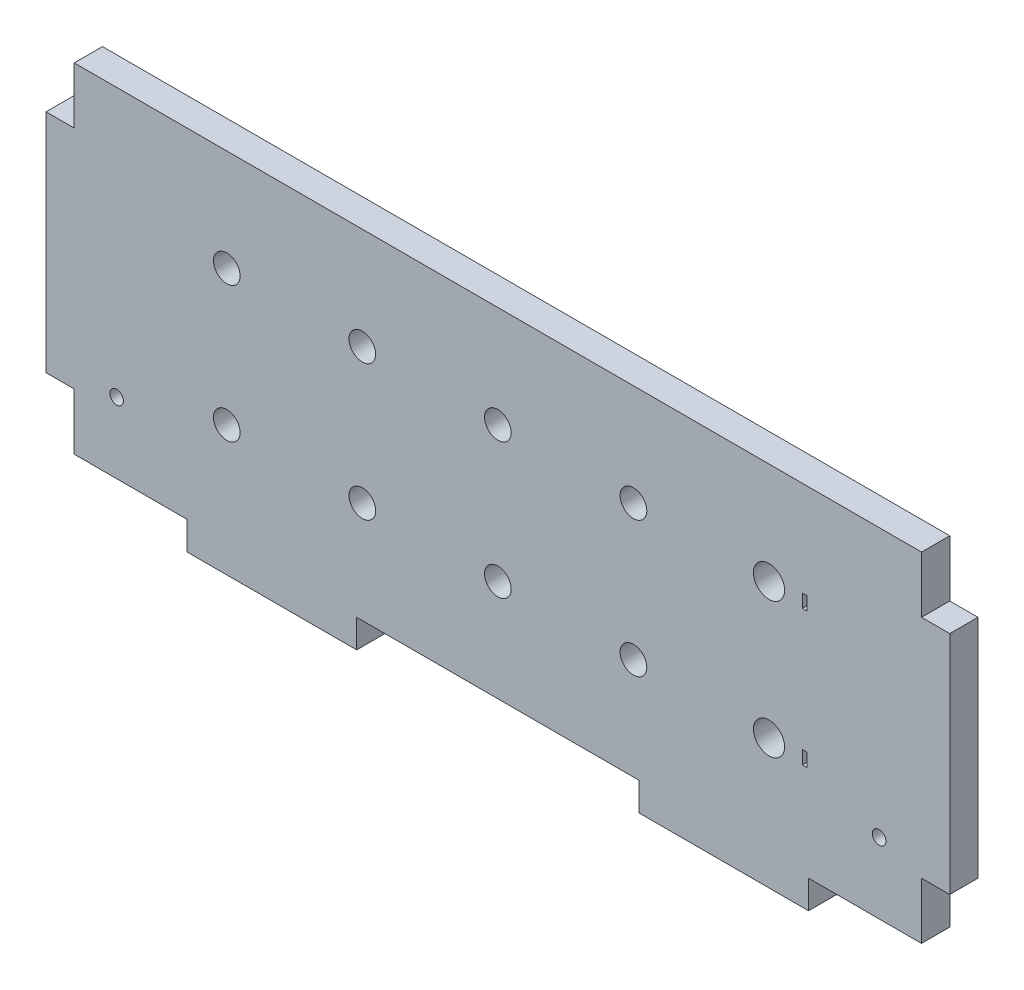
SolidWorks part; units mm, degrees
ref_plane "Front Plane" through (0, 0, 0) normal (0, 0, 1) x (1, 0, 0)
ref_plane "Top Plane" through (0, 0, 0) normal (0, 1, 0) x (1, 0, 0)
ref_plane "Right Plane" through (0, 0, 0) normal (1, 0, 0) x (0, 0, -1)
sketch "Sketch1" plane through (0, 0, 0) normal (0, 0, 1) x (1, 0, 0)
  line L1 (-95.25, -38.1) -> (95.25, -38.1)
  line L2 (-95.25, -38.1) -> (-95.25, 38.1)
  line L3 (-95.25, 38.1) -> (95.25, 38.1)
  line L4 (95.25, -38.1) -> (95.25, 38.1)
  line L5 (-95.25, -38.1) -> (95.25, 38.1) construction
  line L6 (-95.25, 38.1) -> (95.25, -38.1) construction
  point P0 (0, 0)
  dimension "D1" = 190.5
  dimension "D2" = 76.2
extrude "Boss-Extrude1" add sketch "Sketch1" along normal blind 6.35
sketch "Sketch2" plane through (-95.25, 0, 0) normal (-1, 0, 0) x (0, 0, 1)
  line L0 (0, 38.1) -> (0, -38.1) construction
  line L1 (0, 25.4) -> (6.35, 25.4)
  line L2 (0, 25.4) -> (0, -25.4)
  line L3 (0, -25.4) -> (6.35, -25.4)
  line L4 (6.35, 25.4) -> (6.35, -25.4)
  line L5 (6.35, 38.1) -> (6.35, -38.1) construction
  line L6 (6.35, 38.1) -> (0, 38.1) construction
  line L7 (6.35, -38.1) -> (0, -38.1) construction
  dimension "D1" = 12.7
  dimension "D2" = 12.7
extrude "Boss-Extrude2" add sketch "Sketch2" along normal blind 6.35
sketch "Sketch3" plane through (95.25, 0, 0) normal (1, 0, 0) x (0, 0, -1)
  line L0 (-6.35, -38.1) -> (-6.35, 38.1) construction
  line L1 (-6.35, 25.4) -> (0, 25.4)
  line L2 (-6.35, 25.4) -> (-6.35, -25.4)
  line L3 (-6.35, -25.4) -> (0, -25.4)
  line L4 (0, 25.4) -> (0, -25.4)
  line L5 (0, -38.1) -> (0, 38.1) construction
  line L6 (-6.35, 38.1) -> (0, 38.1) construction
  line L7 (-6.35, -38.1) -> (0, -38.1) construction
  dimension "D1" = 12.7
  dimension "D2" = 12.7
extrude "Boss-Extrude3" add sketch "Sketch3" along normal blind 6.35
sketch "Sketch4" plane through (0, -38.1, 0) normal (0, -1, 0) x (1, 0, 0)
  line L0 (-95.25, 6.35) -> (95.25, 6.35) construction
  line L1 (-69.85, 6.35) -> (-31.75, 6.35)
  line L2 (-69.85, 6.35) -> (-69.85, 0)
  line L3 (-69.85, 0) -> (-31.75, 0)
  line L4 (-31.75, 6.35) -> (-31.75, 0)
  line L5 (-95.25, 0) -> (95.25, 0) construction
  line L6 (-95.25, 6.35) -> (-95.25, 0) construction
  line L7 (31.75, 6.35) -> (69.85, 6.35)
  line L8 (31.75, 6.35) -> (31.75, 0)
  line L9 (31.75, 0) -> (69.85, 0)
  line L10 (69.85, 6.35) -> (69.85, 0)
  line L11 (95.25, 6.35) -> (95.25, 0) construction
  point P14 (95.25, 3.175)
  dimension "D1" = 25.4
  dimension "D2" = 25.4
  dimension "D3" = 38.1
  dimension "D4" = 38.1
extrude "Boss-Extrude4" add sketch "Sketch4" along normal blind 6.35
sketch "Sketch7" plane through (0, 0, 0) normal (0, 0, -1) x (-1, 0, 0)
  line L0 (-30.48, 15.24) -> (0, 15.24) construction
  line L1 (-30.48, 15.24) -> (-30.48, -15.24) construction
  line L2 (-95.25, 38.1) -> (95.25, 38.1) construction
  line L3 (-60.96, 15.24) -> (-60.96, -15.24) construction
  line L5 (95.25, -38.1) -> (69.85, -38.1) construction
  line L6 (30.48, 15.24) -> (15.24, 15.24) construction
  line L7 (15.24, 15.24) -> (0, 15.24) construction
  line L8 (0, 15.24) -> (0, 38.1) construction
  line L9 (0, -15.24) -> (0, -38.1) construction
  line L10 (-95.25, -38.1) -> (-95.25, -25.4) construction
  line L11 (101.6, 25.4) -> (101.6, -25.4) construction
  line L12 (-60.96, 15.24) -> (-68.96, 15.24) construction
  line L13 (-68.46, 13.74) -> (-69.46, 13.74)
  line L14 (-68.46, 13.74) -> (-68.46, 16.74)
  line L15 (-68.46, 16.74) -> (-69.46, 16.74)
  line L16 (-69.46, 13.74) -> (-69.46, 16.74)
  line L17 (-68.46, 13.74) -> (-69.46, 16.74) construction
  line L18 (-68.46, 16.74) -> (-69.46, 13.74) construction
  line L19 (-68.96, -15.24) -> (-60.96, -15.24) construction
  line L20 (-69.46, -16.74) -> (-68.46, -16.74)
  line L21 (-69.46, -16.74) -> (-69.46, -13.74)
  line L22 (-69.46, -13.74) -> (-68.46, -13.74)
  line L23 (-68.46, -16.74) -> (-68.46, -13.74)
  line L24 (-69.46, -16.74) -> (-68.46, -13.74) construction
  line L25 (-69.46, -13.74) -> (-68.46, -16.74) construction
  circle A0 centre (-30.48, 15.24) radius 3
  circle A1 centre (0, 15.24) radius 3
  circle A2 centre (30.48, 15.24) radius 3
  circle A3 centre (60.96, 15.24) radius 3
  circle A4 centre (0, -15.24) radius 3
  circle A5 centre (30.48, -15.24) radius 3
  circle A6 centre (60.96, -15.24) radius 3
  circle A7 centre (-30.48, -15.24) radius 3
  circle A8 centre (-60.96, 15.24) radius 3.5
  circle A9 centre (-60.96, -15.24) radius 3.5
  point P30 (0, 38.1)
  point P31 (-60.96, 15.24)
  point P32 (-60.96, -15.24)
  point P39 (-68.96, 15.24)
  point P44 (-64.46, 15.24)
  point P46 (-68.96, -15.24)
  dimension "D1" = 6
  dimension "D7" = 7
  dimension "D4" = 30.48
  dimension "D5" = 30.48
  dimension "D6" = 30.48
  dimension "D8" = 4
  dimension "D9" = 1
  dimension "D10" = 3
  dimension "D11" = 3
  dimension "D2" = 4
  dimension "D3" = 2
extrude "Cut-Extrude1" cut sketch "Sketch7" against normal up to next
extrude "Cut-Extrude2" cut sketch "Sketch8" against normal blind 6.35
sketch "Sketch8" plane through (23.7637, 98.5857, 6.35) normal (0, 0, 1) x (1, 0, 0)
  circle A0 centre (-109.4887, -120.8107) radius 1.524
  circle A2 centre (61.9613, -120.8107) radius 1.524
